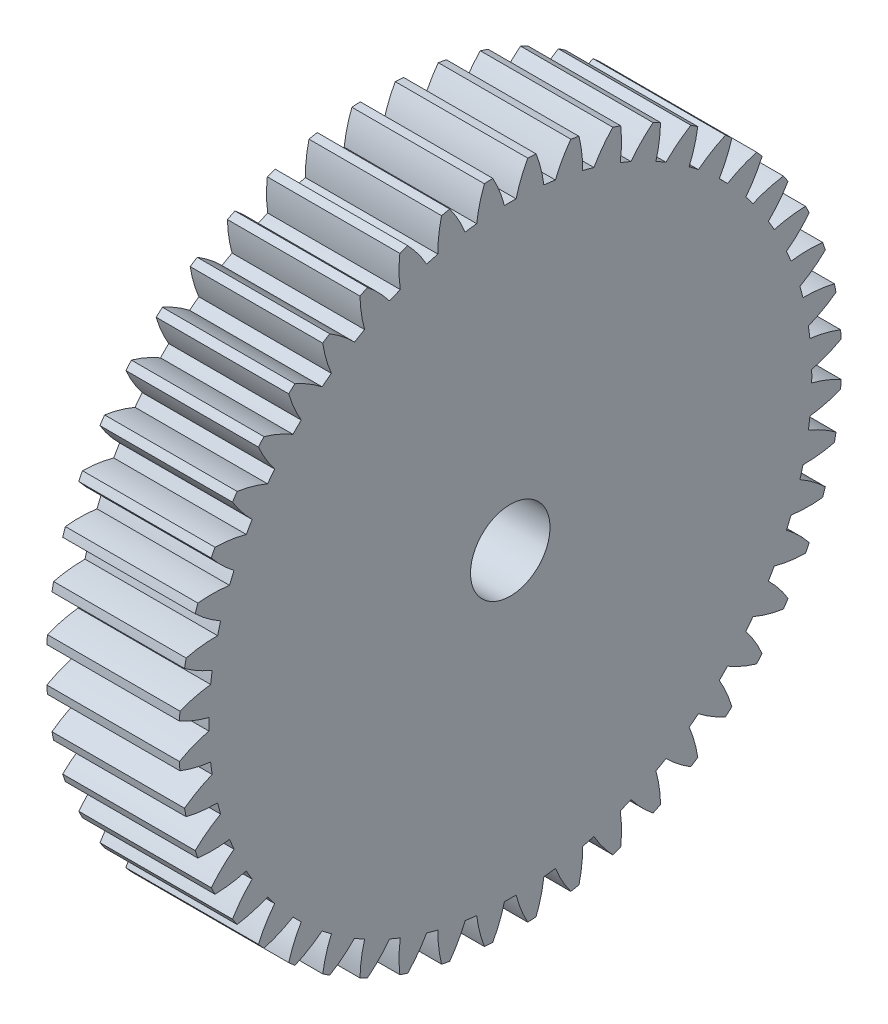
SolidWorks part; units mm, degrees
ref_plane "Plane1" through (0, 0, 0) normal (0, 0, 1) x (1, 0, 0)
ref_plane "Plane2" through (0, 0, 0) normal (0, 1, 0) x (1, 0, 0)
ref_plane "Plane3" through (0, 0, 0) normal (1, 0, 0) x (0, 0, -1)
other "Configuration Table"
sketch "HoldingSke" plane through (0, 0, 0) normal (0, 1, 0) x (1, 0, 0)
  line L0 (0, 0) -> (0.6691, -0.7431)
  line L1 (-15, 0) -> (100, 0) construction
  line L2 (0, 0) -> (-2.1039, 2.3779)
  line L3 (0, 0) -> (-11.863, 4.5341)
  line L4 (0, 0) -> (5.7786, 6.4178)
  line L5 (0, 0) -> (-46.8476, -17.4728)
  line L6 (0, 0) -> (-8.2896, -5.593)
  line L7 (-2.1039, 2.3779) -> (8.6586, 51.2059)
  line L8 (-76.2, 54.61) -> (-75.2, 54.61)
  line L9 (-71.009, 38.7566) -> (-53.1078, 45.2721)
  line L10 (-76.2, 71.12) -> (104.1128, 71.12)
  line L11 (0, 0) -> (-10, 0)
  line L12 (-76.2, 101.6) -> (-76.162, 101.6)
  line L13 (24.9733, 27.94) -> (52.9518, 28.4284)
  line L14 (24.9733, 27.94) -> (24.9743, 27.94)
  line L15 (24.9733, 27.94) -> (100.4006, 29.5858)
  line L16 (-63.627, -1) -> (-12.827, -1)
  circle A0 centre (0, 0) radius 3
  circle A1 centre (0, 0) radius 22.749
  circle A2 centre (0, 0) radius 37.5
  circle A3 centre (0, 0) radius 3
  dimension "MHD" = 45.498
  dimension "Hub_dia" = 75
  dimension "Bore" = 6
  dimension "MBD" = 6
  dimension "Num_teeth" = 48
  dimension "Pitch" = 1
  dimension "Overall_len" = 50
  dimension "Show_teeth" = 48
  dimension "Thickness" = 10
  dimension "OAL" = 50.0001
  dimension "T_dim" = 1
  dimension "Ap" = 20
  dimension "H" = 19.05
  dimension "Pitch_radius" = 180.3128
  dimension "Width" = 10
  dimension "Backlash" = 0.038
  dimension "Addendum_fac" = 1
  dimension "Dedendum_fac" = 1.25
  dimension "Clearance_fac" = 0.25
  dimension "Dedendum_add" = 0.001
  dimension "Module" = 1
sketch "BasProSke" plane through (0, 0, 0) normal (0, 1, 0) x (1, 0, 0)
  line L0 (-10, 0) -> (60, 0) construction
  line L1 (0, 0) -> (0, 25)
  line L2 (0, 0) -> (10, 0)
  line L3 (10, 0) -> (10, 25)
  line L4 (10, 25) -> (0, 25)
  dimension "Thickness" = 10
  dimension "Diameter" = 50
revolve "Base-Revolve" add sketch "BasProSke" angle 360 about L0
sketch "TooCutSke" plane through (0, 0, 0) normal (1, 0, 0) x (0, 0, -1)
  line L1 (0, 0) -> (0, 107) construction
  line L2 (0, 0) -> (-0.8518, 23.9849) construction
  line L3 (0, 0) -> (-3.1379, 47.8757) construction
  line L4 (-0.8518, 23.9849) -> (-1.569, 23.9379) construction
  arc A0 (0.4395, 22.7448) -> (-0.4395, 22.7448) centre (0, 0) ccw
  arc A1 (1.3336, 24.9898) -> (-1.3336, 24.9898) centre (0, 0) ccw
  circle A2 centre (0, 0) radius 24 construction
  circle A3 centre (0, 0) radius 22.5526 construction
  arc A4 (-0.4395, 22.7448) -> (-1.3336, 24.9898) centre (-9.7344, 20.3436) ccw
  arc A5 (1.3336, 24.9898) -> (0.4395, 22.7448) centre (9.7344, 20.3436) ccw
  dimension "Root_dia" = 45.498
  dimension "Overcut_dia" = 50.0508
  dimension "Pitch_dia" = 48
  dimension "Base_dia" = 45.1052
  dimension "Flank_rad" = 9.6
  dimension "Half_ang" = 3.75
  dimension "Half_CT" = 0.7188
extrude "ToothCut" cut sketch "TooCutSke" along normal through all
fillet "Breaks" [suppressed] radius 0.02
fillet "RootFillets" [suppressed] radius 0.251
pattern_circular "TeethCuts" count 48 every 7.5 about axis through (-10, 0, 0) along (1, 0, 0) of "ToothCut", "RootFillets", "Breaks"
sketch "HubNeaOneSke" plane through (0, 0, 0) normal (-1, 0, 0) x (0, 0, 1)
  circle A0 centre (0, 0) radius 22.749
  dimension "Diameter" = 45.498
extrude "HubNearOne" [suppressed] add sketch "HubNeaOneSke" along normal blind 40.0001
sketch "HubNeaBotSke" plane through (0, 0, 0) normal (-1, 0, 0) x (0, 0, 1)
  circle A0 centre (0, 0) radius 22.749
  dimension "Diameter" = 45.498
extrude "HubNearBoth" [suppressed] add sketch "HubNeaBotSke" along normal blind 20
ref_plane "FarPln" through (10, 0, 0) normal (1, 0, 0) x (0, 0, -1)
sketch "HubFarSke" plane through (10, 0, 0) normal (1, 0, 0) x (0, 0, -1)
  circle A0 centre (0, 0) radius 22.749
  dimension "Diameter" = 45.498
extrude "HubFar" [suppressed] add sketch "HubFarSke" along normal blind 20
sketch "BorSke" plane through (0, 0, 0) normal (1, 0, 0) x (0, 0, -1)
  circle A0 centre (0, 0) radius 3
  dimension "Diameter" = 6
extrude "Bore" cut sketch "BorSke" along normal mid plane 100.0001
sketch "KeySke" plane through (0, 0, 0) normal (1, 0, 0) x (0, 0, -1)
  line L0 (-1, 0) -> (-1, 4)
  line L1 (-1, 4) -> (1, 4)
  line L2 (1, 4) -> (1, 0)
  line L3 (0, 0) -> (0, 34) construction
  line L4 (-1, 0) -> (1, 0)
  dimension "Offset" = 4
  dimension "Width" = 2
extrude "Keyway" [suppressed] cut sketch "KeySke" along normal mid plane 100.0001
pattern_circular "Keyway2" [suppressed] count 2 every 90 about axis through (-10, 0, 0) along (1, 0, 0)
equation "' \"Module@HoldingSke\" = 6.35"
equation "' \"Num_teeth@HoldingSke\" = 12"
equation "' \"Ap@HoldingSke\" =  20"
equation "' \"Ap@HoldingSke\" = 20"
equation "' \"Width@HoldingSke\" = 0.5 * 25.4"
equation "' \"Hub_dia@HoldingSke\"= 1 * 25.4"
equation "' \"Hub_dia@HoldingSke\" = 1 * 25.4"
equation "' \"Overall_len@HoldingSke\" = 1.0 * 25.4"
equation "' \"Bore@HoldingSke\" = 0.75 * 25.4"
equation "' \"T_dim@HoldingSke\" = 0.1 * 25.4"
equation "' \"Width@KeySke\" = 0.25 * 25.4"
equation "' \"Show_teeth@HoldingSke\" = 13"
equation "' \"Backlash@HoldingSke\" = 0.009 * 25.4"
equation "' \"Addendum_fac@HoldingSke\" = 1.0"
equation "' \"Dedendum_fac@HoldingSke\" = 1.25"
equation "' \"Dedendum_add@HoldingSke\" = 0.00005 * 25.4"
equation "' \"Clearance_fac@HoldingSke\" = 0.25"
equation "\"Pitch@HoldingSke\" = 1 / \"Module@HoldingSke\""
equation "\"Overcut_dia@TooCutSke\" = (\"Num_teeth@HoldingSke\" + 2 * \"Addendum_fac@HoldingSke\") / \"Pitch@HoldingSke\" + 0.002 * 25.4"
equation "\"Pitch_dia@TooCutSke\" = \"Num_teeth@HoldingSke\" / \"Pitch@HoldingSke\""
equation "\"Base_dia@TooCutSke\" = \"Num_teeth@HoldingSke\" / \"Pitch@HoldingSke\" * cos((\"Ap@HoldingSke\"  * 3.14159265 / 180))"
equation "\"Root_dia@TooCutSke\" = (\"Num_teeth@HoldingSke\" + 2) / \"Pitch@HoldingSke\" - 2 * (\"Addendum_fac@HoldingSke\" + \"Dedendum_fac@HoldingSke\") / \"Pitch@HoldingSke\" - \"Dedendum_add@HoldingSke\" * 2"
equation "\"Half_ang@TooCutSke\" = 180 / \"Num_teeth@HoldingSke\""
equation "\"Half_CT@TooCutSke\" = \"Num_teeth@HoldingSke\" / \"Pitch@HoldingSke\" * sin((3.14159265 / 2 / \"Num_teeth@HoldingSke\")) / 2 - 7 * \"Backlash@HoldingSke\" / 4"
equation "\"Flank_rad@TooCutSke\" = \"Num_teeth@HoldingSke\" / \"Pitch@HoldingSke\" / 5"
equation "\"Radius@RootFillets\" = \"Clearance_fac@HoldingSke\" / \"Pitch@HoldingSke\" + \"Dedendum_add@HoldingSke\""
equation "\"Break_rad@Breaks\" = 0.02 / \"Pitch@HoldingSke\""
equation "\"Thickness@HoldingSke\" = \"Width@HoldingSke\""
equation "\"OAL@HoldingSke\" = \"Thickness@HoldingSke\""
equation "\"MHD@HoldingSke\" = (\"Num_teeth@HoldingSke\" + 2) / \"Pitch@HoldingSke\" - 2 * (\"Addendum_fac@HoldingSke\" + \"Dedendum_fac@HoldingSke\")  / \"Pitch@HoldingSke\" - \"Dedendum_add@HoldingSke\" * 2"
equation "\"MBD@HoldingSke\" = (\"Num_teeth@HoldingSke\" + 2) / \"Pitch@HoldingSke\" - 2 * (\"Addendum_fac@HoldingSke\" + \"Dedendum_fac@HoldingSke\")  / \"Pitch@HoldingSke\" - \"Dedendum_add@HoldingSke\" * 2 - 0.002 * 25.4"
equation "\"MHD@HoldingSke\" = ((sgn( \"MHD@HoldingSke\" - \"Hub_dia@HoldingSke\" )-1)*( \"MHD@HoldingSke\" - \"Hub_dia@HoldingSke\" ))/-2+ \"Hub_dia@HoldingSke\""
equation "\"MBD@HoldingSke\" = ((sgn( \"MBD@HoldingSke\" - \"Bore@HoldingSke\" )-1)*( \"MBD@HoldingSke\" - \"Bore@HoldingSke\" ))/-2+ \"Bore@HoldingSke\""
equation "\"OAL@HoldingSke\" = ((sgn( \"OAL@HoldingSke\" - \"Overall_len@HoldingSke\" )+1)*( \"OAL@HoldingSke\" - \"Overall_len@HoldingSke\" ))/2 + \"Overall_len@HoldingSke\" + 0.000002 * 25.4"
equation "\"Num_teeth@TeethCuts\" = int( \"Show_teeth@HoldingSke\" ) + 1"
equation "\"Num_teeth@TeethCuts\" = ((sgn( \"Num_teeth@TeethCuts\" - \"Num_teeth@HoldingSke\" )-1)*( \"Num_teeth@TeethCuts\" - \"Num_teeth@HoldingSke\" ))/-2+ \"Num_teeth@HoldingSke\""
equation "\"Num_teeth@TeethCuts\" = ((sgn( \"Num_teeth@TeethCuts\" - 2.0)+1)*( \"Num_teeth@TeethCuts\" - 2.0))/2 +2.0"
equation "\"Angle@TeethCuts\" = 360.0 / \"Num_teeth@HoldingSke\""
equation "\"Diameter@BasProSke\" = (\"Num_teeth@HoldingSke\" + 2 * \"Addendum_fac@HoldingSke\") / \"Pitch@HoldingSke\""
equation "\"Thickness@BasProSke\"  = \"Thickness@HoldingSke\""
equation "' \"Fillet_rad@BasProSke\" =  \"Thickness@HoldingSke\" * 0.05"
equation "' \"Fillet_rad@BasProSke\" = \"Thickness@HoldingSke\" * 0.05"
equation "\"MHD@HoldingSke\" = ((sgn( \"MHD@HoldingSke\" - \"Root_dia@TooCutSke\" )-1)*( \"MHD@HoldingSke\" - \"Root_dia@TooCutSke\" ))/-2+ \"Root_dia@TooCutSke\""
equation "\"Diameter@HubNeaOneSke\" = \"MHD@HoldingSke\""
equation "\"Length@HubNearOne\" = \"OAL@HoldingSke\" - \"Thickness@BasProSke\""
equation "\"Diameter@HubNeaBotSke\" = \"MHD@HoldingSke\""
equation "\"Length@HubNearBoth\" = ( \"OAL@HoldingSke\" - \"Thickness@BasProSke\" ) / 2.0"
equation "\"Thickness@FarPln\" = \"Thickness@BasProSke\""
equation "\"Diameter@HubFarSke\" = \"MHD@HoldingSke\""
equation "\"Length@HubFar\" = ( \"OAL@HoldingSke\" - \"Thickness@BasProSke\" ) / 2.0"
equation "\"Diameter@BorSke\" = \"MBD@HoldingSke\""
equation "\"D1@Bore\" = \"OAL@HoldingSke\" * 2.0"
equation "\"D1@Keyway\" = \"OAL@HoldingSke\" * 2.0"
equation "\"Offset@KeySke\" = \"T_dim@HoldingSke\" + \"MBD@HoldingSke\" / 2.0"
